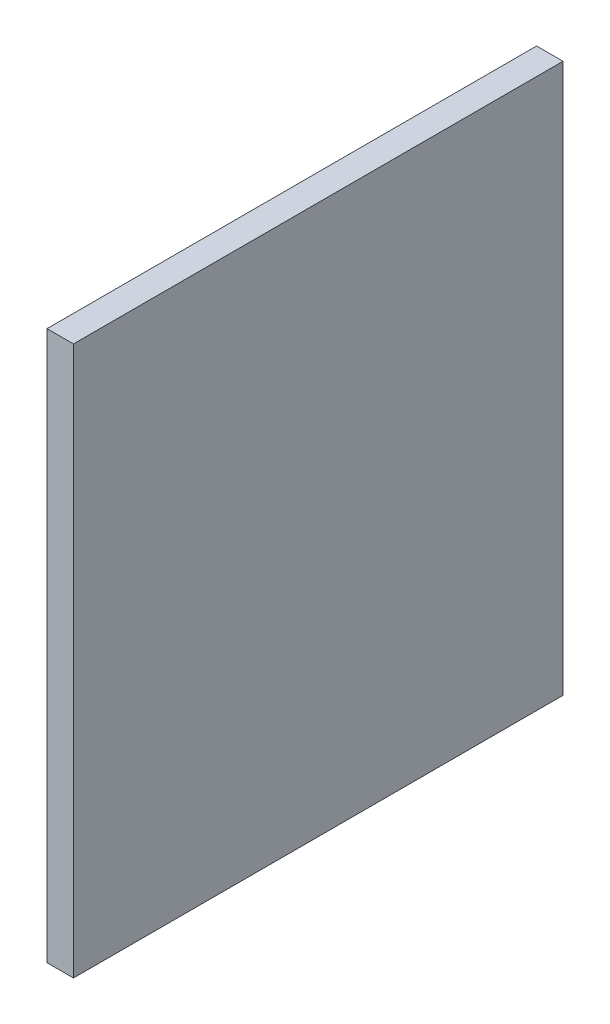
SolidWorks part; units mm, degrees
material "Mahogany"
ref_plane "Front Plane" through (0, 0, 0) normal (0, 0, 1) x (1, 0, 0)
ref_plane "Top Plane" through (0, 0, 0) normal (0, 1, 0) x (1, 0, 0)
ref_plane "Right Plane" through (0, 0, 0) normal (1, 0, 0) x (0, 0, -1)
sketch "Sketch1" plane through (0, 0, 0) normal (1, 0, 0) x (0, 0, -1)
  line L1 (148, -166) -> (-148, -166)
  line L2 (148, -166) -> (148, 166)
  line L3 (148, 166) -> (-148, 166)
  line L4 (-148, -166) -> (-148, 166)
  line L5 (148, -166) -> (-148, 166) construction
  line L6 (148, 166) -> (-148, -166) construction
  point P0 (0, 0)
  dimension "D1" = 332
  dimension "D2" = 296
extrude "Boss-Extrude1" add sketch "Sketch1" along normal blind 16
